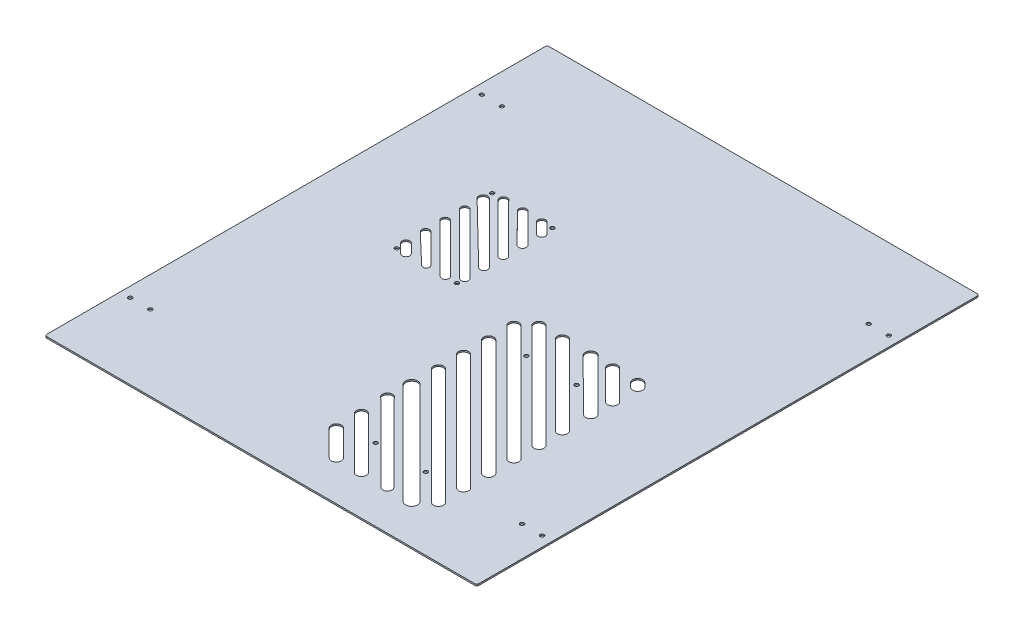
SolidWorks part; units mm, degrees
ref_plane "Front Plane" through (0, 0, 0) normal (0, 0, 1) x (1, 0, 0)
ref_plane "Top Plane" through (0, 0, 0) normal (0, 1, 0) x (1, 0, 0)
ref_plane "Right Plane" through (0, 0, 0) normal (1, 0, 0) x (0, 0, -1)
other "Center of Mass"
sketch "Sketch1" plane through (0, 0, 0) normal (0, 1, 0) x (1, 0, 0)
  line L1 (-215, -250) -> (215, -250)
  line L2 (-215, -250) -> (-215, 250)
  line L3 (-215, 250) -> (215, 250)
  line L4 (215, -250) -> (215, 250)
  line L5 (-215, -250) -> (215, 250) construction
  line L6 (-215, 250) -> (215, -250) construction
  point P0 (0, 0)
  dimension "D1" = 430
  dimension "D2" = 500
extrude "Boss-Extrude1" add sketch "Sketch1" along normal blind 1.5
sketch "Sketch6" plane through (0, 1.5, 0) normal (0, 1, 0) x (1, 0, 0)
  circle A0 centre (92.2927, -28) radius 1.95
  circle A1 centre (42.2927, -28) radius 1.95
  circle A2 centre (92.2927, -178) radius 1.95
  circle A3 centre (42.2927, -178) radius 1.95
  dimension "D1" = 50
  dimension "D2" = 150
sketch "Sketch7" plane through (0, 1.5, 0) normal (0, 1, 0) x (1, 0, 0)
  circle A0 centre (-114.98, 95.1924) radius 1.95
  circle A1 centre (-54.98, 95.1924) radius 1.95
  circle A2 centre (-54.98, 0.1924) radius 1.95
  circle A3 centre (-114.98, 0.1924) radius 1.95
  dimension "D1" = 95
  dimension "D2" = 60
sketch "Sketch12" plane through (0, 0, 0) normal (0, -1, 0) x (-1, 0, 0)
  line L2 (215, 250) -> (215, -250) construction
  line L3 (-215, -250) -> (-215, 250) construction
  circle A0 centre (-185, -175) radius 1.95
  circle A1 centre (-205, 170) radius 1.95
  circle A5 centre (-205, -175) radius 1.95
  circle A6 centre (-185, 170) radius 1.95
  circle A7 centre (205, -175) radius 1.95
  circle A9 centre (185, 175) radius 1.95
  circle A10 centre (205, 175) radius 1.95
  circle A11 centre (185, -175) radius 1.95
  dimension "D5" = 10
  dimension "D6" = 20
  dimension "D7" = 20
  dimension "D8" = 10
extrude "Cut-Extrude3" cut sketch "Sketch12" against normal blind 50.8
extrude "Cut-Extrude4" cut sketch "Sketch6" against normal blind 50.8
extrude "Cut-Extrude5" cut sketch "Sketch7" against normal blind 50.8
fillet "Fillet1" radius 2 4 edges at (215, 0.75, -250) (215, 0.75, 250) (-215, 0.75, 250) (-215, 0.75, -250)
sketch "Sketch13" plane through (0, 0, 0) normal (0, -1, 0) x (1, 0, 0)
  line L0 (67.2927, 28) -> (67.2927, 178) construction
  line L6 (92.2927, 178) -> (42.2927, 178) construction
  line L8 (92.2927, 178) -> (92.2927, 28) construction
  line L9 (92.2927, 28) -> (42.2927, 28) construction
  line L10 (42.2927, 178) -> (42.2927, 28) construction
  line L11 (67.2927, 103) -> (42.2927, 103) construction
  line L12 (124.7927, 122.9451) -> (9.7927, 7.9451) construction
  line L13 (124.7927, 210.5) -> (9.7927, 210.5)
  line L14 (124.7927, 210.5) -> (124.7927, -4.5)
  line L15 (124.7927, -4.5) -> (9.7927, -4.5)
  line L16 (9.7927, 210.5) -> (9.7927, -4.5)
  line L17 (124.7927, 210.5) -> (9.7927, -4.5) construction
  line L18 (124.7927, -4.5) -> (9.7927, 210.5) construction
  line L19 (128.3282, 119.4095) -> (13.3282, 4.4095)
  line L20 (121.2572, 126.4806) -> (6.2572, 11.4806)
  line L21 (124.7927, 147.9451) -> (9.7927, 32.9451) construction
  line L22 (128.3282, 144.4095) -> (13.3282, 29.4095)
  line L23 (121.2572, 151.4806) -> (6.2572, 36.4806)
  line L26 (124.7927, 172.9451) -> (9.7927, 57.9451) construction
  line L29 (128.3282, 169.4095) -> (13.3282, 54.4095)
  line L32 (121.2572, 176.4806) -> (6.2572, 61.4806)
  line L35 (124.7927, 197.9451) -> (9.7927, 82.9451) construction
  line L38 (128.3282, 194.4095) -> (13.3282, 79.4095)
  line L41 (121.2572, 201.4806) -> (6.2572, 86.4806)
  line L44 (110.6506, 210.5) -> (9.7927, 109.6421) construction
  line L47 (114.8916, 206.259) -> (14.0337, 105.4011)
  line L50 (102.1686, 210.5) -> (5.5517, 113.8831)
  line L53 (-54.98, -95.1924) -> (-114.98, -95.1924) construction
  line L58 (-114.98, -95.1924) -> (-114.98, -44.2867) construction
  line L62 (86.5307, 210.5) -> (8.6916, 132.661) construction
  line L65 (-114.98, -0.1924) -> (-54.98, -0.1924) construction
  line L66 (-54.98, -0.1924) -> (-54.98, -95.1924) construction
  line L67 (-54.98, -84.5868) -> (-65.5855, -95.1924) construction
  line L68 (-54.98, -89.8901) -> (-60.2822, -95.1924)
  line L69 (-57.6303, -81.9365) -> (-68.2358, -92.5421)
  line L70 (-54.98, -95.1924) -> (-114.98, -0.1924) construction
  line L71 (-54.98, -65.4331) -> (-84.7393, -95.1924) construction
  line L72 (-54.98, -70.7364) -> (-79.4324, -95.1924)
  line L73 (-57.6384, -62.7886) -> (-87.2428, -92.5491)
  line L74 (-54.98, -46.2793) -> (-103.893, -95.1924) construction
  line L75 (-54.98, -51.5826) -> (-98.5897, -95.1924)
  line L76 (-57.6398, -43.6363) -> (-106.2442, -92.5505)
  line L77 (-54.98, -27.1256) -> (-120.2706, -91.5396) construction
  line L78 (-54.98, -32.4289) -> (-111.9255, -89.3745)
  line L79 (-57.5955, -24.4383) -> (-117.9928, -83.2246)
  line L80 (-52.4189, -5.4139) -> (-114.98, -67.9718) construction
  line L81 (-52.3742, -10.6694) -> (-112.3283, -70.6235)
  line L83 (-63.9533, 2.3637) -> (-114.98, -48.8181) construction
  line L84 (-63.9494, -2.7446) -> (-112.3283, -51.1235)
  line L87 (-71.6576, -0.1924) -> (-114.98, -43.5148)
  line L88 (-85.508, -0.1924) -> (-114.98, -29.6644) construction
  line L91 (-83.2026, -2.4978) -> (-112.3283, -31.6235)
  line L92 (-90.2324, -0.1924) -> (-114.98, -23.7903)
  line L93 (-105.7005, -0.1924) -> (-114.98, -10.5106) construction
  line L96 (-103.0489, -2.844) -> (-112.3283, -12.1235)
  line L99 (-111.0038, -0.1924) -> (-114.98, -4.1685)
  line L102 (-60.2822, -95.1924) -> (-62.9366, -97.844)
  line L105 (-98.5897, -95.1924) -> (-100.7736, -97.6705)
  line L106 (-79.4324, -95.1924) -> (-81.8594, -97.7646)
  line L107 (-114.98, -62.6685) -> (-117.6316, -65.3202)
  line L108 (-114.98, -43.5148) -> (-117.4324, -45.635)
  line L109 (-114.98, -4.1685) -> (-117.6316, -6.8202)
  line L110 (-54.98, -89.8901) -> (-52.3283, -87.2358)
  line L111 (-54.98, -70.7364) -> (-52.3283, -68.0843)
  line L112 (-54.98, -51.5826) -> (-52.3283, -48.9306)
  line L113 (-54.98, -32.4289) -> (-52.3283, -29.7772)
  line L114 (-57.5857, -5.4578) -> (-114.98, -62.6685)
  line L115 (-90.2324, -0.1924) -> (-87.7579, 2.1672)
  line L116 (-71.6576, -0.1924) -> (-69.0283, 2.3851)
  line L117 (-111.0038, -0.1924) -> (-108.3522, 2.4593)
  line L118 (-114.98, -23.7903) -> (-117.5678, -26.2579)
  line L119 (89.7127, 207.318) -> (13.4147, 131.0201)
  line L120 (80.1667, 210.5) -> (7.0508, 137.3841)
  line L121 (60.6506, 210.5) -> (9.7927, 159.6421) construction
  line L122 (64.1861, 206.9645) -> (13.3282, 156.1066)
  line L123 (53.5795, 210.5) -> (6.2572, 163.1777)
  line L124 (35.6506, 210.5) -> (9.7927, 184.6421) construction
  line L125 (39.1861, 206.9645) -> (13.3282, 181.1066)
  line L126 (28.5795, 210.5) -> (6.2572, 188.1777)
  line L127 (10.6506, 210.5) -> (9.7927, 209.6421) construction
  line L128 (16.6674, 209.4458) -> (13.3282, 206.1066)
  line L130 (128.3284, -3.8936) -> (124.1859, -8.0357)
  line L133 (125.6429, 98.792) -> (22.3509, -4.5) construction
  line L134 (129.1784, 95.2564) -> (29.422, -4.5)
  line L135 (122.1073, 102.3275) -> (18.8154, -0.9645)
  line L136 (124.7927, 74.6421) -> (45.6506, -4.5) construction
  line L137 (128.3282, 71.1066) -> (52.7216, -4.5)
  line L138 (121.2572, 78.1777) -> (42.115, -0.9645)
  line L139 (124.7927, 46.436) -> (73.8567, -4.5) construction
  line L140 (128.4341, 42.7783) -> (80.9436, -4.5)
  line L141 (121.1513, 50.0937) -> (70.1015, -0.728)
  line L142 (124.7927, 24.6421) -> (95.6506, -4.5) construction
  line L143 (128.3282, 21.1066) -> (102.7216, -4.5)
  line L144 (121.2572, 28.1777) -> (92.115, -0.9645)
  line L145 (124.7928, -0.358) -> (120.6506, -4.5) construction
  line L147 (121.2572, 3.1777) -> (117.115, -0.9645)
  line L166 (6.6802, 213.5553) -> (10.376, 216.4949)
  line L167 (28.5795, 210.5) -> (32.115, 214.0355)
  line L168 (53.5795, 210.5) -> (57.115, 214.0355)
  line L169 (80.1667, 210.5) -> (83.3487, 213.682)
  line L170 (102.1686, 210.5) -> (106.4096, 214.741)
  line L171 (102.7216, -4.5) -> (99.1861, -8.0355)
  line L172 (80.9436, -4.5) -> (77.854, -8.0143)
  line L173 (52.7216, -4.5) -> (49.1861, -8.0355)
  line L174 (29.422, -4.5) -> (25.8864, -8.0355)
  line L392 (124.7927, 347.9451) -> (9.7927, 232.9451) construction
  line L393 (128.3282, 344.4095) -> (13.3282, 229.4095) [skipped]
  line L394 (121.2572, 351.4806) -> (6.2572, 236.4806) [skipped]
  line L395 (124.7927, 322.9451) -> (9.7927, 207.9451) construction
  line L396 (128.3282, 319.4095) -> (13.3282, 204.4095) [skipped]
  line L397 (121.2572, 326.4806) -> (6.2572, 211.4806) [skipped]
  line L398 (124.7927, 297.9451) -> (9.7927, 182.9451) construction
  line L399 (128.3282, 294.4095) -> (13.3282, 179.4095) [skipped]
  line L400 (121.2572, 301.4806) -> (6.2572, 186.4806) [skipped]
  line L401 (124.7927, 272.9451) -> (9.7927, 157.9451) construction
  line L402 (128.3282, 269.4095) -> (13.3282, 154.4095) [skipped]
  line L403 (121.2572, 276.4806) -> (6.2572, 161.4806) [skipped]
  line L404 (124.7927, 247.9451) -> (9.7927, 132.9451) construction
  line L405 (128.3282, 244.4095) -> (13.3282, 129.4095) [skipped]
  line L406 (121.2572, 251.4806) -> (6.2572, 136.4806) [skipped]
  line L407 (124.7927, 222.9451) -> (9.7927, 107.9451) construction
  line L408 (128.3282, 219.4095) -> (13.3282, 104.4095) [skipped]
  line L409 (121.2572, 226.4806) -> (6.2572, 111.4806) [skipped]
  line L410 (124.7927, 347.9451) -> (9.7927, 232.9451) construction
  line L411 (128.3282, 344.4095) -> (13.3282, 229.4095) [skipped]
  line L412 (121.2572, 351.4806) -> (6.2572, 236.4806) [skipped]
  line L413 (124.7927, 322.9451) -> (9.7927, 207.9451) construction
  line L414 (128.3282, 319.4095) -> (13.3282, 204.4095) [skipped]
  line L415 (121.2572, 326.4806) -> (6.2572, 211.4806) [skipped]
  line L416 (124.7927, 297.9451) -> (9.7927, 182.9451) construction
  line L417 (128.3282, 294.4095) -> (13.3282, 179.4095) [skipped]
  line L418 (121.2572, 301.4806) -> (6.2572, 186.4806) [skipped]
  line L419 (124.7927, 272.9451) -> (9.7927, 157.9451) construction
  line L420 (128.3282, 269.4095) -> (13.3282, 154.4095) [skipped]
  line L421 (121.2572, 276.4806) -> (6.2572, 161.4806) [skipped]
  line L422 (124.7927, 247.9451) -> (9.7927, 132.9451) construction
  line L423 (128.3282, 244.4095) -> (13.3282, 129.4095) [skipped]
  line L424 (121.2572, 251.4806) -> (6.2572, 136.4806) [skipped]
  line L425 (124.7927, 222.9451) -> (9.7927, 107.9451) construction
  line L426 (128.3282, 219.4095) -> (13.3282, 104.4095) [skipped]
  line L427 (121.2572, 226.4806) -> (6.2572, 111.4806) [skipped]
  arc A32 (128.3282, 119.4095) -> (121.2572, 126.4806) centre (124.7927, 122.9451) ccw
  arc A59 (-68.2358, -92.5421) -> (-62.9366, -97.844) centre (-65.5855, -95.1924) ccw
  arc A60 (-87.2428, -92.5491) -> (-81.8594, -97.7646) centre (-84.5855, -95.1924) ccw
  arc A61 (-106.2442, -92.5505) -> (-100.7736, -97.6705) centre (-103.5855, -95.1924) ccw
  arc A63 (-117.6316, -65.3202) -> (-112.3283, -70.6235) centre (-114.98, -67.9718) ccw
  arc A64 (-117.4324, -45.635) -> (-112.3283, -51.1235) centre (-114.98, -48.4718) ccw
  arc A65 (-117.5678, -26.2579) -> (-112.3283, -31.6235) centre (-114.98, -28.9718) ccw
  arc A66 (-117.6316, -6.8202) -> (-112.3283, -12.1235) centre (-114.98, -9.4718) ccw
  arc A67 (-52.3283, -29.7772) -> (-57.5955, -24.4383) centre (-54.98, -27.1256) ccw
  arc A68 (-52.3283, -48.9306) -> (-57.6398, -43.6363) centre (-54.98, -46.2793) ccw
  arc A69 (-52.3283, -68.0843) -> (-57.6384, -62.7886) centre (-54.98, -65.4331) ccw
  arc A70 (-52.3283, -87.2358) -> (-57.6303, -81.9365) centre (-54.98, -84.5868) ccw
  arc A71 (-52.3742, -10.6694) -> (-57.5857, -5.4578) centre (-54.98, -8.0636) ccw
  arc A72 (-117.9928, -83.2246) -> (-111.9255, -89.3745) centre (-114.98, -86.32) ccw
  arc A73 (6.2572, 11.4806) -> (13.3282, 4.4095) centre (9.7927, 7.9451) ccw
  arc A74 (128.3282, 144.4095) -> (121.2572, 151.4806) centre (124.7927, 147.9451) ccw
  arc A75 (6.2572, 36.4806) -> (13.3282, 29.4095) centre (9.7927, 32.9451) ccw
  arc A76 (128.3282, 169.4095) -> (121.2572, 176.4806) centre (124.7927, 172.9451) ccw
  arc A77 (6.2572, 61.4806) -> (13.3282, 54.4095) centre (9.7927, 57.9451) ccw
  circle A78 centre (-122.5855, -95.1924) radius 3.7481 [skipped]
  arc A79 (-83.2026, -2.4978) -> (-87.7579, 2.1672) centre (-85.508, -0.1924) ccw
  arc A80 (-103.0489, -2.844) -> (-108.3522, 2.4593) centre (-105.7005, -0.1924) ccw
  arc A81 (-63.9494, -2.7446) -> (-69.0283, 2.3851) centre (-66.5016, -0.1924) ccw
  arc A82 (128.3282, 194.4095) -> (121.2572, 201.4806) centre (124.7927, 197.9451) ccw
  arc A83 (6.2572, 86.4806) -> (13.3282, 79.4095) centre (9.7927, 82.9451) ccw
  arc A85 (5.5517, 113.8831) -> (14.0337, 105.4011) centre (9.7927, 109.6421) ccw
  arc A87 (7.0508, 137.3841) -> (13.4147, 131.0201) centre (8.6916, 132.661) ccw
  arc A89 (6.2572, 163.1777) -> (13.3282, 156.1066) centre (9.7927, 159.6421) ccw
  arc A91 (6.2572, 188.1777) -> (13.3282, 181.1066) centre (9.7927, 184.6421) ccw
  arc A93 (6.6802, 213.5553) -> (13.3282, 206.1066) centre (9.7927, 209.6421) ccw
  arc A96 (129.1784, 95.2564) -> (122.1073, 102.3275) centre (125.6429, 98.792) ccw
  arc A98 (128.3282, 71.1066) -> (121.2572, 78.1777) centre (124.7927, 74.6421) ccw
  arc A100 (128.4341, 42.7783) -> (121.1513, 50.0937) centre (124.7927, 46.436) ccw
  arc A102 (128.3282, 21.1066) -> (121.2572, 28.1777) centre (124.7927, 24.6421) ccw
  arc A104 (128.3284, -3.8936) -> (121.2572, 3.1777) centre (124.7928, -0.358) ccw
  arc A118 (117.115, -0.9645) -> (124.1859, -8.0357) centre (120.6506, -4.5) ccw
  arc A119 (92.115, -0.9645) -> (99.1861, -8.0355) centre (95.6506, -4.5) ccw
  arc A120 (70.1015, -0.728) -> (77.854, -8.0143) centre (73.8567, -4.5) ccw
  arc A121 (42.115, -0.9645) -> (49.1861, -8.0355) centre (45.6506, -4.5) ccw
  arc A122 (18.8154, -0.9645) -> (25.8864, -8.0355) centre (22.3509, -4.5) ccw
  arc A123 (114.8916, 206.259) -> (106.4096, 214.741) centre (110.6506, 210.5) ccw
  arc A124 (89.7127, 207.318) -> (83.3487, 213.682) centre (86.5307, 210.5) ccw
  arc A125 (64.1861, 206.9645) -> (57.115, 214.0355) centre (60.6506, 210.5) ccw
  arc A126 (39.1861, 206.9645) -> (32.115, 214.0355) centre (35.6506, 210.5) ccw
  arc A127 (16.6674, 209.4458) -> (10.376, 216.4949) centre (13.3216, 212.7917) ccw
  arc A285 (128.3282, 344.4095) -> (121.2572, 351.4806) centre (124.7927, 347.9451) ccw [skipped]
  arc A286 (6.2572, 236.4806) -> (13.3282, 229.4095) centre (9.7927, 232.9451) ccw [skipped]
  arc A287 (128.3282, 319.4095) -> (121.2572, 326.4806) centre (124.7927, 322.9451) ccw [skipped]
  arc A288 (6.2572, 211.4806) -> (13.3282, 204.4095) centre (9.7927, 207.9451) ccw [skipped]
  arc A289 (128.3282, 294.4095) -> (121.2572, 301.4806) centre (124.7927, 297.9451) ccw [skipped]
  arc A290 (6.2572, 186.4806) -> (13.3282, 179.4095) centre (9.7927, 182.9451) ccw [skipped]
  arc A291 (128.3282, 269.4095) -> (121.2572, 276.4806) centre (124.7927, 272.9451) ccw [skipped]
  arc A292 (6.2572, 161.4806) -> (13.3282, 154.4095) centre (9.7927, 157.9451) ccw [skipped]
  arc A293 (128.3282, 244.4095) -> (121.2572, 251.4806) centre (124.7927, 247.9451) ccw [skipped]
  arc A294 (6.2572, 136.4806) -> (13.3282, 129.4095) centre (9.7927, 132.9451) ccw [skipped]
  arc A295 (128.3282, 219.4095) -> (121.2572, 226.4806) centre (124.7927, 222.9451) ccw [skipped]
  arc A296 (6.2572, 111.4806) -> (13.3282, 104.4095) centre (9.7927, 107.9451) ccw [skipped]
  point P18 (67.2927, 65.4451)
  point P23 (67.2927, 90.4451)
  point P30 (67.2927, 115.4451)
  point P37 (67.2927, 140.4451)
  point P46 (67.2927, 167.1421)
  point P54 (67.2927, 192.1421)
  point P73 (67.2927, 217.1421)
  point P85 (67.2927, 153)
  point P89 (-59.0853, -88.6922)
  point P94 (67.2927, 42.1421)
  point P102 (67.2927, 17.1421)
  point P116 (67.2927, 193)
  point P124 (-66.4512, -76.9043)
  point P125 (67.2927, 173)
  point P135 (-73.8171, -65.1165)
  point P151 (-81.183, -53.3286)
  point P153 (67.2927, 193)
  point P156 (67.2927, 292.1421)
  point P159 (-88.5489, -41.5407)
  point P160 (67.2927, 173)
  point P167 (67.2927, 153)
  point P168 (-95.9147, -29.7529)
  point P174 (67.2927, 193)
  point P176 (-103.2806, -17.965)
  point P181 (67.2927, 173)
  point P184 (-110.6465, -6.1771)
  point P188 (67.2927, 153)
  point P207 (67.2927, 267.1421)
  point P227 (67.2927, 242.1421)
  point P235 (67.2927, 192.1421)
  point P242 (67.2927, 167.1421)
  point P251 (67.2927, 193)
  point P258 (67.2927, 173)
  point P265 (67.2927, 153)
  point P272 (67.2927, 193)
  point P279 (67.2927, 173)
  point P286 (67.2927, 153)
  point P321 (67.2927, 193)
  point P328 (67.2927, 173)
  point P335 (67.2927, 153)
  point P342 (67.2927, 193)
  point P349 (67.2927, 173)
  point P356 (67.2927, 153)
  point P365 (67.2927, 193)
  point P372 (67.2927, 173)
  point P379 (67.2927, 153)
  point P386 (67.2927, 193)
  point P393 (67.2927, 173)
  point P400 (67.2927, 153)
  point P407 (67.2927, 193)
  point P414 (67.2927, 173)
  point P421 (67.2927, 153)
  point P428 (67.2927, 193)
  point P435 (67.2927, 173)
  point P442 (67.2927, 153)
  point P449 (67.2927, 193)
  point P456 (67.2927, 173)
  point P463 (67.2927, 153)
  point P470 (67.2927, 193)
  point P477 (67.2927, 173)
  point P484 (67.2927, 153)
  point P491 (67.2927, 193)
  point P498 (67.2927, 173)
  point P505 (67.2927, 153)
  point P512 (67.2927, 193)
  point P519 (67.2927, 173)
  point P526 (67.2927, 153)
  point P533 (67.2927, 193)
  point P540 (67.2927, 173)
  point P547 (67.2927, 153)
  point P554 (67.2927, 193)
  point P561 (67.2927, 173)
  point P568 (67.2927, 153)
  point P575 (67.2927, 193)
  point P582 (67.2927, 173)
  point P589 (67.2927, 153)
  point P596 (67.2927, 193)
  point P603 (67.2927, 173)
  point P610 (67.2927, 153)
  point P617 (67.2927, 193)
  point P624 (67.2927, 173)
  point P631 (67.2927, 153)
  point P638 (67.2927, 193)
  point P645 (67.2927, 173)
  point P652 (67.2927, 153)
  point P677 (67.2927, 292.1421)
  point P684 (67.2927, 267.1421)
  point P691 (67.2927, 242.1421)
  point P698 (67.2927, 217.1421)
  point P705 (67.2927, 192.1421)
  point P712 (67.2927, 167.1421)
  point P719 (67.2927, 288.6066)
  point P726 (67.2927, 263.6066)
  point P733 (67.2927, 238.6066)
  point P740 (67.2927, 213.6066)
  point P747 (67.2927, 188.6066)
  point P754 (67.2927, 163.6066)
  point P761 (67.2927, 288.6066)
  point P768 (67.2927, 263.6066)
  point P775 (67.2927, 238.6066)
  point P782 (67.2927, 213.6066)
  point P789 (67.2927, 188.6066)
  point P796 (67.2927, 163.6066)
  point P803 (67.2927, 288.6066)
  point P810 (67.2927, 263.6066)
  point P817 (67.2927, 238.6066)
  point P824 (67.2927, 213.6066)
  point P831 (67.2927, 188.6066)
  point P838 (67.2927, 163.6066)
  point P845 (67.2927, 288.6066)
  point P852 (67.2927, 263.6066)
  point P859 (67.2927, 238.6066)
  point P866 (67.2927, 213.6066)
  point P873 (67.2927, 188.6066)
  point P880 (67.2927, 163.6066)
  point P887 (67.2927, 288.6066)
  point P894 (67.2927, 263.6066)
  point P901 (67.2927, 238.6066)
  point P908 (67.2927, 213.6066)
  point P915 (67.2927, 188.6066)
  point P922 (67.2927, 163.6066)
  point P929 (67.2927, 288.6066)
  point P936 (67.2927, 263.6066)
  point P943 (67.2927, 238.6066)
  point P950 (67.2927, 213.6066)
  point P957 (67.2927, 188.6066)
  point P964 (67.2927, 163.6066)
  point P971 (67.2927, 289.3137)
  point P978 (67.2927, 264.3137)
  point P985 (67.2927, 239.3137)
  point P992 (67.2927, 214.3137)
  point P999 (67.2927, 189.3137)
  point P1006 (67.2927, 164.3137)
  point P1013 (67.2927, 289.3137)
  point P1020 (67.2927, 264.3137)
  point P1027 (67.2927, 239.3137)
  point P1034 (67.2927, 214.3137)
  point P1041 (67.2927, 189.3137)
  point P1048 (67.2927, 164.3137)
  point P1055 (67.2927, 290.4451)
  point P1062 (67.2927, 265.4451)
  point P1069 (67.2927, 240.4451)
  point P1076 (67.2927, 215.4451)
  point P1083 (67.2927, 190.4451)
  point P1090 (67.2927, 165.4451)
  point P1097 (67.2927, 290.4451)
  point P1104 (67.2927, 265.4451)
  point P1111 (67.2927, 240.4451)
  point P1118 (67.2927, 215.4451)
  point P1125 (67.2927, 190.4451)
  point P1132 (67.2927, 165.4451)
  point P1139 (67.2927, 290.4451)
  point P1146 (67.2927, 265.4451)
  point P1153 (67.2927, 240.4451)
  point P1160 (67.2927, 215.4451)
  point P1167 (67.2927, 190.4451)
  point P1174 (67.2927, 165.4451)
  point P1181 (67.2927, 290.4451)
  point P1188 (67.2927, 265.4451)
  point P1195 (67.2927, 240.4451)
  point P1202 (67.2927, 215.4451)
  point P1209 (67.2927, 190.4451)
  point P1216 (67.2927, 165.4451)
  point P1223 (67.2927, 290.4451)
  point P1230 (67.2927, 265.4451)
  point P1237 (67.2927, 240.4451)
  point P1244 (67.2927, 215.4451)
  point P1251 (67.2927, 190.4451)
  point P1258 (67.2927, 165.4451)
  dimension "D1" = 115
  dimension "D5" = 45
  dimension "D6" = 4
  dimension "D7" = 4
  dimension "D8" = 45
  dimension "D9" = 3.8
  dimension "D10" = 10
  dimension "D2" = 215
  dimension "D3" = 45
  dimension "D4" = 5
  dimension "D11" = 7.68
  dimension "D12" = 10
  dimension "D13" = 9
  dimension "D14" = 45
  dimension "D15" = 45
  dimension "D16" = 5
  dimension "D17" = 3.8
extrude "Cut-Extrude6" cut sketch "Sketch13" against normal blind 10
scale "Scale1" scale about centroid uniform scaling yes scale factor 0.76
